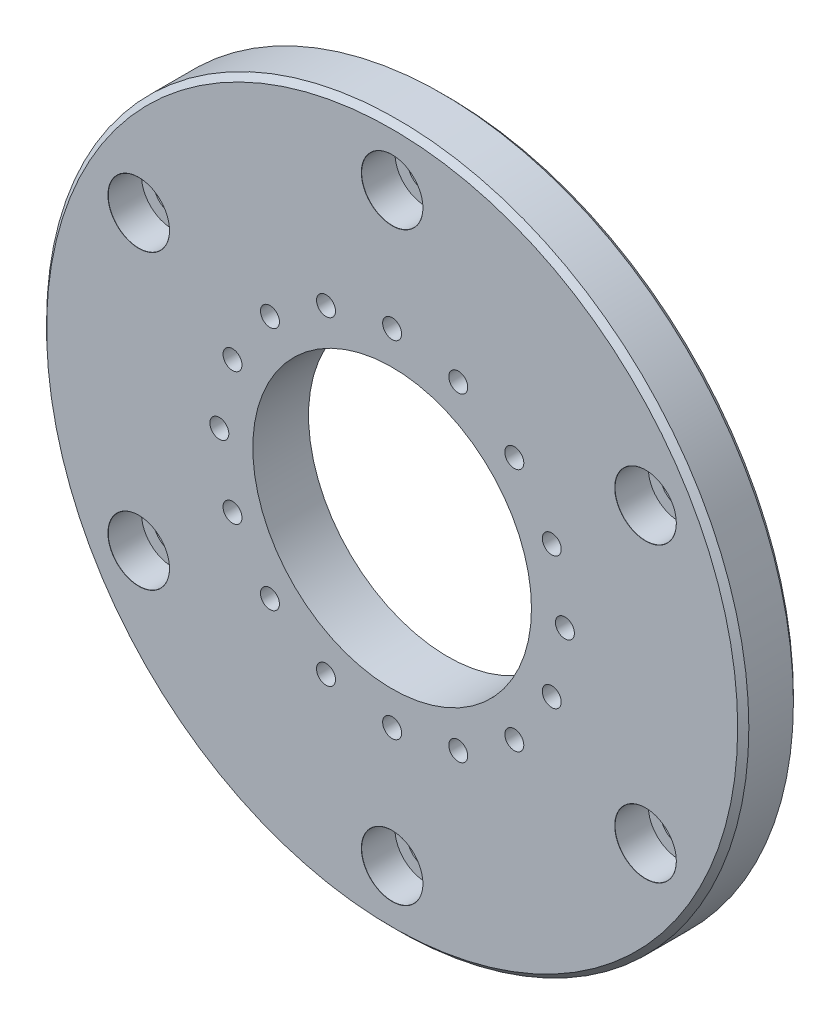
SolidWorks part; units mm, degrees
ref_plane "前基準面" through (0, 0, 0) normal (0, 0, 1) x (1, 0, 0)
ref_plane "上基準面" through (0, 0, 0) normal (0, 1, 0) x (1, 0, 0)
ref_plane "右基準面" through (0, 0, 0) normal (1, 0, 0) x (0, 0, -1)
sketch "Sketch1" plane through (0, 0, 0) normal (0, 0, 1) x (1, 0, 0)
  circle A0 centre (-200, 0) radius 63
  circle A1 centre (-200, 0) radius 25 construction
  arc A2 (-170.7963, 41.8108) -> (-170.7963, -41.8108) centre (-200, 0) ccw construction
  arc A3 (-170.7963, 41.8108) -> (-170.7963, -41.8108) centre (-200, 0) ccw construction
  arc A5 (-247.122, -41.8153) -> (-152.878, -41.8153) centre (-200, 0) ccw construction
  circle A6 centre (-200, 0) radius 25
sketch "Sketch2" plane through (0, 0, 0) normal (0, 0, 1) x (1, 0, 0)
  circle A0 centre (-200, 0) radius 63 construction
  circle A1 centre (-200, 0) radius 63
extrude "Boss-Extrude1" add sketch "Sketch2" along normal blind 10
sketch "Sketch4" plane through (0, 0, 10) normal (0, 0, 1) x (1, 0, 0)
  circle A0 centre (-200, 0) radius 25 construction
  circle A1 centre (-200, 0) radius 25
extrude "Cut-Extrude1" cut sketch "Sketch4" against normal through all
hole_wizard "CBORE for M8 Socket Head Cap Screw1" positions "Sketch7" profile "Sketch6" counterbore size "M6" standard "JIS"
sketch "Sketch7" plane through (0, 0, 10) normal (0, 0, 1) x (1, 0, 0)
  line L0 (-200, 52.5) -> (-200, 0) construction
  point P0 (-200, 52.5)
sketch "Sketch6" plane through (-200, 52.5, 10) normal (1, 0, 0) x (0, -1, 0)
  line L0 (0, 0) -> (0, 19)
  line L1 (0, 19) -> (3.3, 17.0172)
  line L2 (3.3, 17.0172) -> (3.3, 6)
  line L3 (3.3, 6) -> (5.5, 6)
  line L5 (5.5, 6) -> (5.5, 0.025)
  line L6 (5.5, 0.025) -> (5.525, 0)
  line L7 (5.525, 0) -> (0, 0)
  line L8 (-5.5, 0.025) -> (-5.525, 0) construction
  line L10 (0, 19) -> (-3.3, 17.0172) construction
  line L11 (0, -6.35) -> (0, 107.95) construction
  dimension "Hole Dia." = 6.6
  dimension "Hole Depth" = 19
  dimension "C'Bore Dia." = 11
  dimension "C'Bore Depth" = 6
  dimension "Near C'Sink Dia." = 11.05
  dimension "Near C'Sink Angle" = 90
  dimension "Drill Angle" = 118
pattern_circular "CirPattern1" count 6 every 60 about axis through (-200, 0, 0) along (0, 0, 1) of "CBORE for M8 Socket Head Cap Screw1"
hole_wizard "CBORE for M3 Socket Head Cap Screw2" positions "Sketch10" profile "Sketch11" counterbore size "M3" standard "JIS" end condition through all
sketch "Sketch10" plane through (0, 0, 0) normal (0, 0, -1) x (-1, 0, 0)
  point P3 (200, 31)
  point P6 (188.1368, 28.6403)
  point P9 (178.0797, 21.9203)
  point P12 (171.3597, 11.8632)
  point P15 (169, 0)
  point P18 (171.3597, -11.8632)
  point P21 (178.0797, -21.9203)
  point P24 (188.1368, -28.6403)
  point P27 (200, -31)
  point P30 (211.8632, -28.6403)
  point P33 (221.9203, -21.9203)
  point P36 (228.6403, -11.8632)
  point P39 (231, 0)
  point P42 (228.6403, 11.8632)
  point P45 (221.9203, 21.9203)
  point P48 (211.8632, 28.6403)
sketch "Sketch11" plane through (-200, 31, 0) normal (1, 0, 0) x (0, 1, 0)
  line L0 (0, 0) -> (0, 10)
  line L1 (0, 10) -> (1.7, 10)
  line L3 (1.7, 10) -> (1.7, 3)
  line L4 (3.25, 3) -> (1.7, 3)
  line L5 (3.25, 3) -> (3.25, 0.025)
  line L6 (3.25, 0.025) -> (3.275, 0)
  line L7 (3.275, 0) -> (0, 0)
  line L8 (-3.25, 0.025) -> (-3.275, 0) construction
  line L11 (0, -6.35) -> (0, 107.95) construction
  dimension "Thru Hole Dia." = 3.4
  dimension "Thru Hole Depth" = 10
  dimension "C'Bore Dia." = 6.5
  dimension "C'Bore Depth" = 3
  dimension "Near C'Sink Dia." = 6.55
  dimension "Near C'Sink Angle" = 90
chamfer "Chamfer1" distance 1 angle 45 2 edges at (-137, 0, 10) (-137, 0, 0)
